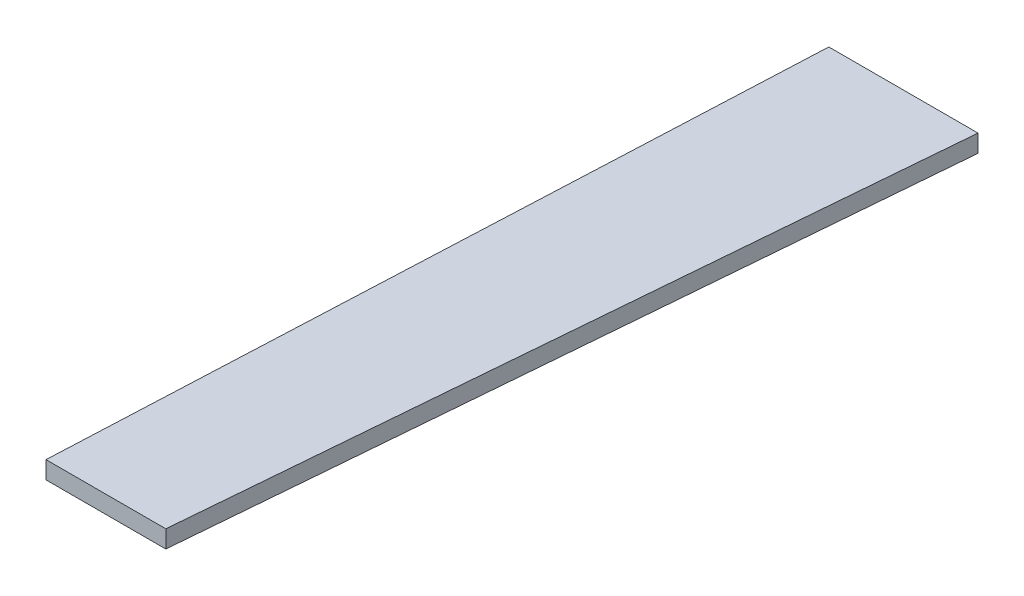
SolidWorks part; units mm, degrees
ref_plane "Front Plane" through (0, 0, 0) normal (0, 0, 1) x (1, 0, 0)
ref_plane "Top Plane" through (0, 0, 0) normal (0, 1, 0) x (1, 0, 0)
ref_plane "Right Plane" through (0, 0, 0) normal (1, 0, 0) x (0, 0, -1)
sketch "Sketch1" plane through (0, 0, 0) normal (0, 1, 0) x (1, 0, 0)
  line L0 (-19.3954, -426.72) -> (48.8714, -426.72)
  line L1 (48.8714, -426.72) -> (85.0098, 0)
  line L2 (85.0098, 0) -> (0, 0)
  line L3 (0, 0) -> (-19.3954, -426.72)
  line L4 (168.8089, -14.2962) -> (116.1659, -438.2005) construction
  line L5 (85.0098, 0) -> (168.8089, -14.2962) construction
  line L6 (116.1659, -438.2005) -> (48.8714, -426.72) construction
  line L7 (85.0098, 0) -> (104.725, -3.3634) construction
  line L8 (104.725, -3.3634) -> (175.9953, -15.5222) construction
  line L9 (175.9953, -15.5222) -> (123.3523, -439.4265) construction
  line L10 (123.3523, -439.4265) -> (68.5866, -430.0834) construction
  line L11 (68.5866, -430.0834) -> (48.8714, -426.72) construction
  line L12 (104.725, -3.3634) -> (68.5866, -430.0834) construction
  point P4 (110.3868, -437.2146)
  point P12 (126.121, -438.2005)
  dimension "D1" = 85.0098
  dimension "D2" = 68.2668
  dimension "D3" = 19.3954
  dimension "D4" = 426.72
  dimension "D5" = 20
  dimension "D6" = 20
  dimension "D7" = 72.3
  dimension "D8" = 142.7477
  dimension "D9" = 175.9953
  dimension "D10" = 439.4265
extrude "Boss-Extrude1" add sketch "Sketch1" along normal blind 10
